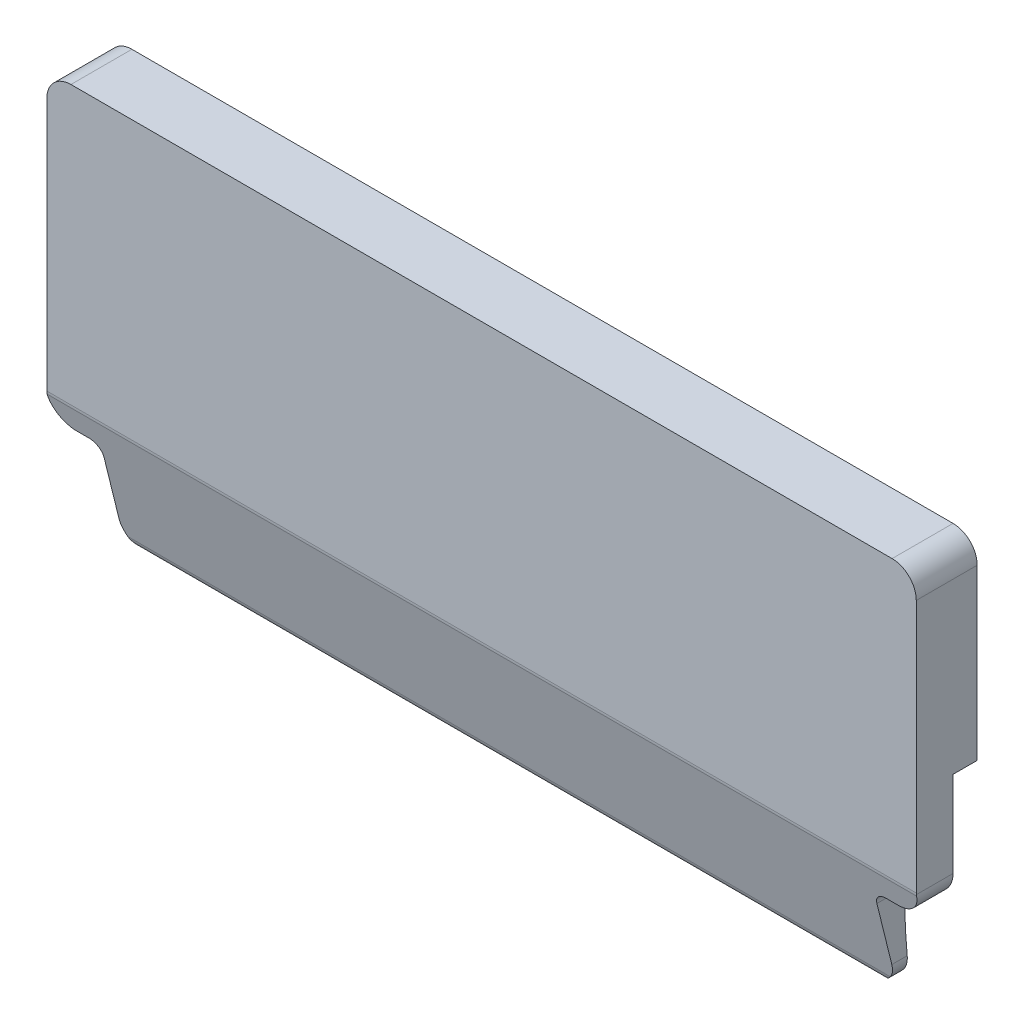
SolidWorks part; units mm, degrees
ref_plane "Front Plane" through (0, 0, 0) normal (0, 0, 1) x (1, 0, 0)
ref_plane "Top Plane" through (0, 0, 0) normal (0, 1, 0) x (1, 0, 0)
ref_plane "Right Plane" through (0, 0, 0) normal (1, 0, 0) x (0, 0, -1)
sketch "Sketch1" plane through (0, 0, 0) normal (0, 0, 1) x (1, 0, 0)
  line L1 (-18, 9.3045) -> (-18, 10.3045)
  line L2 (18, 9.3035) -> (18, 17.3035)
  line L3 (18, 9.3035) -> (18, 6.7512)
  line L4 (-18, 10.3045) -> (-18, 17.3035)
  line L5 (17, 5.7512) -> (16.5, 5.7512)
  line L6 (16, 5.2512) -> (16, 2.7512)
  line L7 (15, 1.7512) -> (-15, 1.7512)
  line L9 (17, 18.3035) -> (-17, 18.3035)
  line L10 (-16, 5.2512) -> (-16, 2.7512)
  line L11 (-17, 5.7512) -> (-16.5, 5.7512)
  line L12 (-18, 9.3045) -> (-18, 6.7512)
  arc A0 (18, 6.7512) -> (17, 5.7512) centre (17, 6.7512) cw
  arc A2 (16, 2.7512) -> (15, 1.7512) centre (15, 2.7512) cw
  arc A3 (16, 5.2512) -> (16.5, 5.7512) centre (16.5, 5.2512) cw
  arc A4 (-16, 5.2512) -> (-16.5, 5.7512) centre (-16.5, 5.2512) ccw
  arc A5 (-16, 2.7512) -> (-15, 1.7512) centre (-15, 2.7512) ccw
  arc A7 (-18, 6.7512) -> (-17, 5.7512) centre (-17, 6.7512) ccw
  arc A8 (18, 17.3035) -> (17, 18.3035) centre (17, 17.3035) ccw
  arc A9 (-18, 17.3035) -> (-17, 18.3035) centre (-17, 17.3035) cw
  point P37 (-16, 5.7512)
  point P38 (-18, 10.3045)
  point P39 (-18, 5.7512)
  dimension "D1" = 1
extrude "Boss-Extrude1" add sketch "Sketch1" along normal blind 1.5 and the other way blind 1.2
sketch "Sketch3" plane through (18, 0, 0) normal (1, 0, 0) x (0, 0, -1)
  line L1 (0.0238, 5.7545) -> (0.0238, 10.3045)
  line L3 (0.2373, 1.7512) -> (0.1268, 1.7512)
  line L4 (0.0238, 10.3045) -> (1.0238, 10.3045)
  line L7 (-1.5, 6.812) -> (-1.5, 1.7512)
  line L9 (0.2373, 1.7512) -> (1.2709, 1.7512)
  line L10 (1.2, 1.7512) -> (-1.5, 1.7512) construction
  line L11 (-1.5, 10.3045) -> (0.0238, 10.3045)
  line L12 (1.2709, 1.7512) -> (1.2709, 10.3045)
  line L13 (0.0238, 10.3045) -> (-1.5, 10.3045)
  line L14 (-1.5, 10.3045) -> (-1.5, 6.812)
  line L15 (-1.4854, 6.6921) -> (-0.3586, 2.1312)
  line L17 (-1.5, 1.7512) -> (0.1268, 1.7512)
  line L18 (0.0238, 10.3051) -> (0.0238, 10.3045)
  line L19 (1, 10.3051) -> (-1.5, 10.3051) construction
  line L20 (1.0238, 10.3045) -> (1.0238, 22.6808)
  line L21 (1.2709, 10.3045) -> (1.2709, 10.3051)
  arc A0 (0.0238, 5.7545) -> (0.2373, 1.7512) centre (25.9469, 5.1296) ccw
  arc A2 (-1.5, 6.812) -> (-1.4854, 6.6921) centre (-1, 6.812) ccw
  arc A3 (-0.3586, 2.1312) -> (0.1268, 1.7512) centre (0.1268, 2.2512) ccw
  arc A4 (1.0238, 22.6808) -> (1.2709, 10.3051) centre (1.0238, 16.4905) cw
  point P28 (-1.5, 6.7512)
  point P31 (-0.2647, 1.7512)
  dimension "D1" = 4.55
extrude "Cut-Extrude1" cut sketch "Sketch3" against normal blind 40
sketch "Sketch6" plane through (-18, 0, 0) normal (-1, 0, 0) x (0, 0, 1)
  line L0 (-1.0238, 10.3045) -> (-1.0238, 12.6345)
  line L1 (-1.0238, 17.3035) -> (-1.0238, 10.3045) construction
sketch "Sketch7" plane through (-18, 0, 0) normal (-1, 0, 0) x (0, 0, 1)
  line L0 (-1.0238, 10.3045) -> (1.3872, 3.6805)
  line L1 (-1.0238, 10.3045) -> (-1.0238, 12.6345)
  line L2 (-1.0238, 17.3035) -> (-1.0238, 10.3045) construction
sketch "Sketch8" plane through (0, 0, -1.0238) normal (0, 0, -1) x (-1, 0, 0)
  line L1 (0, 10.3045) -> (0, 12.6345)
  line L2 (18, 10.3045) -> (-18, 10.3045) construction
  line L3 (0, 12.6345) -> (0, 13.8645)
  circle A0 centre (0, 13.8645) radius 1.23
sketch "Sketch10" plane through (18, 0, 0) normal (1, 0, 0) x (0, 0, -1)
  line L1 (1.0238, 10.3045) -> (1.0238, 17.3035) construction
  line L2 (1.0238, 13.804) -> (12.7887, 9.5219) construction
sketch "Sketch11" plane through (0, 0, -1.0238) normal (0, 0, -1) x (-1, 0, 0)
  line L0 (0, 10.3045) -> (0, 15.2945)
  line L2 (18, 10.3045) -> (-18, 10.3045) construction
  line L3 (-11, 15.2945) -> (11, 15.2945)
  circle A0 centre (11, 15.2945) radius 1
  circle A1 centre (-11, 15.2945) radius 1
  circle A2 centre (0, 15.2945) radius 2.5
  dimension "D1" = 2
  dimension "D4" = 5
  dimension "D2" = 11
  dimension "D3" = 4.99
sketch "Sketch12" plane through (18, 0, 0) normal (1, 0, 0) x (0, 0, -1)
  line L0 (1.0238, 10.3045) -> (1.0238, 15.2945)
  line L1 (1.0238, 10.3045) -> (1.0238, 17.3035) construction
  line L2 (1.0238, 15.2945) -> (6.2899, 13.3778)
  dimension "D1" = 4.99
ref_plane "Plane1" through (0, 0.8764, 2.4078) normal (0, -0.342, -0.9397) x (1, 0, 0)
sketch "Sketch15" plane through (0, 0.8764, 2.4078) normal (0, -0.342, -0.9397) x (1, 0, 0)
  line L0 (0, -10.0333) -> (0, -15.0333)
  line L1 (-18, -10.0333) -> (18, -10.0333) construction
  circle A1 centre (0, -15.0333) radius 2.45
  dimension "D2" = 4.9
  dimension "D1" = 5
sketch "Sketch16" plane through (0, 0, 0) normal (1, 0, 0) x (0, 0, -1)
  line L0 (1.0238, 10.3045) -> (1.0238, 15.3085)
  line L1 (1.0238, 10.3045) -> (1.0238, 17.3035) construction
  line L2 (1.0238, 15.3085) -> (6.662, 13.2563)
  line L3 (1.0238, 15.3085) -> (1.0238, 12.8065)
  line L5 (6.662, 10.7613) -> (6.662, 13.2563)
  line L6 (6.662, 10.7613) -> (1.0238, 12.8065)
  dimension "D1" = 2.495
revolve "Revolve1" [suppressed] add sketch "Sketch16" angle 360 about L2
sketch "Sketch17" plane through (0, 0, -1.0238) normal (0, 0, -1) x (-1, 0, 0)
sketch "Sketch18" [suppressed] plane through (0, 0, 0) normal (1, 0, 0) x (0, 0, -1)
  line L0 (1.0238, 15.3085) -> (1.0238, 17.8035)
  line L1 (1.0238, 17.3035) -> (1.0238, 18.3035) construction
  line L2 (1.0238, 17.8035) -> (2.632, 17.2251)
  line L4 (1.0238, 15.3085) -> (7.4638, 12.9645)
  line L5 (6.662, 10.7613) -> (8.2657, 15.1676) construction
  line L6 (2.632, 17.2251) -> (1.8279, 15.0158)
  line L7 (1.0238, 12.8065) -> (2.632, 17.2251) construction
  line L8 (2.632, 17.2251) -> (1.0238, 15.3085)
  dimension "D1" = 2.495
ref_plane "Plane2" through (0, 0, -1.0238) normal (0, 0, -1) x (-1, 0, 0)
extrude "Cut-Extrude2" [suppressed] cut sketch "Sketch11" against normal blind 5
